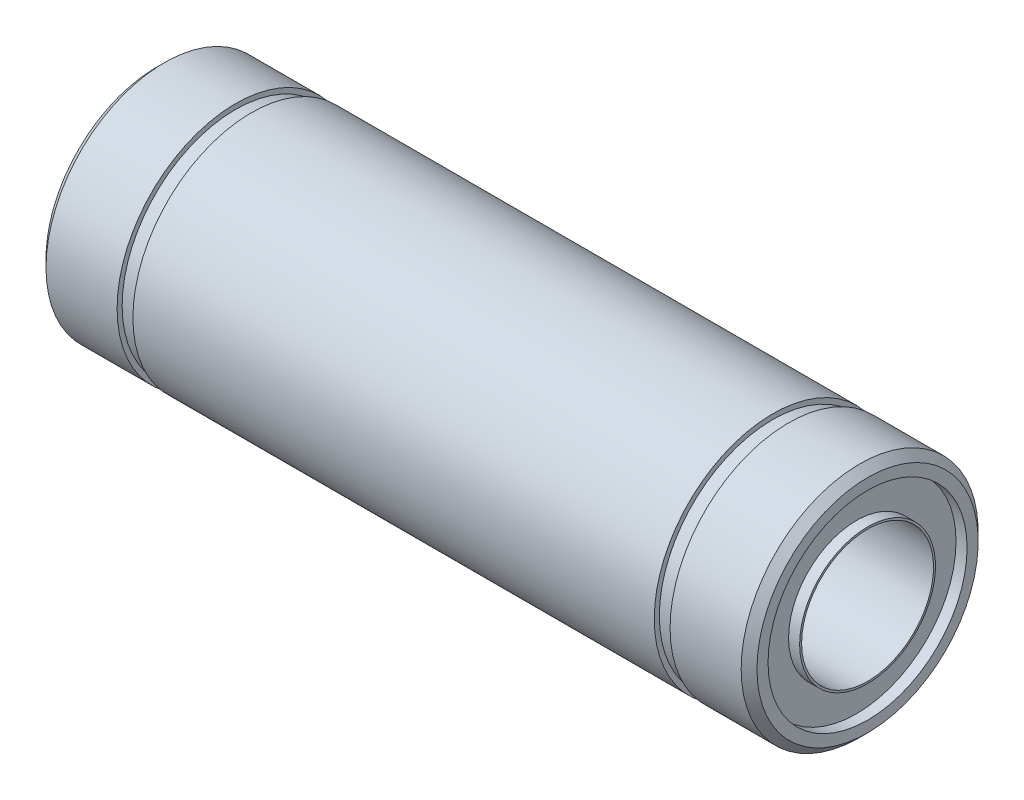
SolidWorks part; units mm, degrees
material "1023 Plech z uhlíkaté oceli (SS)"
ref_plane "Front Plane" through (0, 0, 0) normal (0, 0, 1) x (1, 0, 0)
ref_plane "Top Plane" through (0, 0, 0) normal (0, 1, 0) x (1, 0, 0)
ref_plane "Right Plane" through (0, 0, 0) normal (1, 0, 0) x (0, 0, -1)
sketch "Skica1" plane through (0, 0, 0) normal (0, 0, 1) x (1, 0, 0)
  line L0 (0, 0) -> (22.3333, 0) construction
  line L1 (0, 4.3) -> (0, 4.175)
  line L2 (0, 7.5) -> (5, 7.5)
  line L3 (0, 7.5) -> (0, 6.3)
  line L4 (0, 4.175) -> (45, 4.175)
  line L5 (45, 7.5) -> (45, 6.3)
  line L6 (0, 6.3) -> (0.7, 6.3)
  line L7 (6, 7.5) -> (39, 7.5)
  line L8 (0, 4.3) -> (0.7, 4.3)
  line L9 (0.7, 6.3) -> (0.7, 4.3)
  line L10 (40, 7.5) -> (45, 7.5)
  line L11 (5, 7.5) -> (5, 7.18)
  line L12 (5, 7.18) -> (6, 7.18)
  line L13 (6, 7.5) -> (6, 7.18)
  line L14 (45, 4.3) -> (45, 4.175)
  line L15 (39, 7.5) -> (39, 7.18)
  line L16 (39, 7.18) -> (40, 7.18)
  line L17 (40, 7.5) -> (40, 7.18)
  line L18 (45, 6.3) -> (44.3, 6.3)
  line L20 (45, 4.3) -> (44.3, 4.3)
  line L21 (44.3, 6.3) -> (44.3, 4.3)
  dimension "D1" = 15
  dimension "D2" = 8.35
  dimension "D3" = 12.6
  dimension "D4" = 8.6
  dimension "D5" = 0.7
  dimension "D6" = 45
  dimension "D7" = 5
  dimension "D8" = 5
  dimension "D9" = 1
  dimension "D10" = 0.32
revolve "Rotovat1" add sketch "Skica1" angle 360 about L0
chamfer "Zkosení1" distance 0.5 angle 45 2 edges at (45, 0, 7.5) (0, 0, 7.5)
